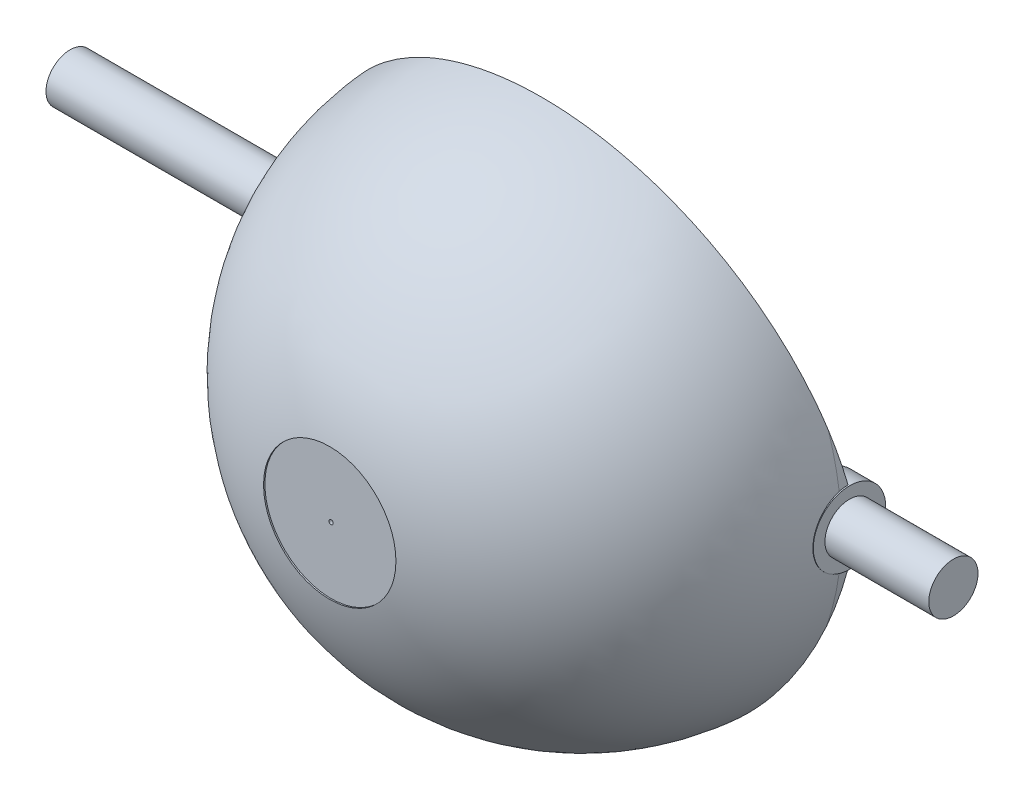
SolidWorks part; units mm, degrees
ref_plane "Front Plane" through (0, 0, 0) normal (0, 0, 1) x (1, 0, 0)
ref_plane "Top Plane" through (0, 0, 0) normal (0, 1, 0) x (1, 0, 0)
ref_plane "Right Plane" through (0, 0, 0) normal (1, 0, 0) x (0, 0, -1)
sketch "Sketch1" plane through (0, 0, 0) normal (0, 0, 1) x (1, 0, 0)
  circle A0 centre (0, 0) radius 27.95
extrude "Boss-Extrude1" add sketch "Sketch1" along normal blind 27.6202
fillet "Fillet1" radius 26.67 1 edges at (27.95, 0, 27.6202)
shell "Shell1" thickness 1.778
sketch "Sketch3" plane through (0, 0, 0) normal (0, 0, -1) x (-1, 0, 0)
  line L1 (-28.5123, -1.3772) -> (-25.5345, -1.3772)
  line L2 (-28.5123, -1.3772) -> (-28.5123, 1.3772)
  line L3 (-28.5123, 1.3772) -> (-25.5345, 1.3772)
  line L4 (-25.5345, -1.3772) -> (-25.5345, 1.3772)
  line L5 (-28.5123, -1.3772) -> (-25.5345, 1.3772) construction
  line L6 (-28.5123, 1.3772) -> (-25.5345, -1.3772) construction
  point P0 (-27.0234, 0)
extrude "Boss-Extrude3" add sketch "Sketch3" along normal blind 1.016
sketch "Sketch4" plane through (28.5123, 0, 0) normal (1, 0, 0) x (0, 0, -1)
  circle A0 centre (0, 0) radius 3.8203
extrude "Boss-Extrude4" add sketch "Sketch4" against normal blind 82.9108 and the other way blind 10.2887 contours A0
sketch "Sketch5" plane through (-54.3985, 0, 0) normal (-1, 0, 0) x (0, 0, 1)
  circle A1 centre (0, 0) radius 0.2185
extrude "Cut-Extrude1" cut sketch "Sketch5" against normal blind 74.422
sketch "Sketch6" plane through (-54.3985, 0, 0) normal (-1, 0, 0) x (0, 0, 1)
  circle A0 centre (0, 0) radius 4.4527
  circle A1 centre (0, 0) radius 2.5419
extrude "Cut-Extrude2" cut sketch "Sketch6" against normal blind 26.4656 contours A1 | A0
sketch "Sketch7" plane through (38.8009, 0, 0) normal (1, 0, 0) x (0, 0, -1)
  circle A0 centre (0, 0) radius 4.5798
  circle A1 centre (0, 0) radius 2.5953
extrude "Cut-Extrude3" cut sketch "Sketch7" against normal blind 10.9598 contours A1 | A0
sketch "Sketch9" plane through (0, 0, 0) normal (0, 0, -1) x (-1, 0, 0)
  circle A0 centre (0, 0) radius 25.3275
extrude "Cut-Extrude4" cut sketch "Sketch9" against normal blind 4.572 and the other way blind 8.128
sketch "Sketch10" plane through (0, 0, 27.6202) normal (0, 0, 1) x (1, 0, 0)
  circle A0 centre (0, 0) radius 0.2266
extrude "Cut-Extrude5" cut sketch "Sketch10" against normal blind 5.588 contours A0
sketch3d "3DSketch1"
  circle A0 centre (0, 0, 27.5994) radius 0.2266 construction
  point P2 (0, 0, 27.3728)
sketch "Sketch11" plane through (0, 0, 27.5994) normal (0, 0, 1) x (1, 0, 0)
  circle A0 centre (0, 0) radius 0.9577
extrude "Boss-Extrude5" add sketch "Sketch11" against normal blind 22.86 separate body contours A0
sketch "Sketch12" plane through (0, 0, 4.7394) normal (0, 0, -1) x (-1, 0, 0)
  line L0 (0, 0) -> (0, 16.6384)
  line L1 (0, 16.6384) -> (11.938, 16.6384)
  line L2 (0, 0) -> (0, -16.6384)
  line L3 (0, -16.6384) -> (-11.9535, -16.6384)
  circle A0 centre (11.938, 16.6384) radius 3.048
  circle A1 centre (-11.9535, -16.6384) radius 3.048
extrude "Boss-Extrude6" add sketch "Sketch12" against normal blind 10.7843 separate body contours A0 | A1
sketch "Sketch14" plane through (0, 0, 0) normal (0, 0, -1) x (-1, 0, 0)
  circle A0 centre (0, 0) radius 27.95
  circle A1 centre (0, 0) radius 2.1119
extrude "Cut-Extrude6" cut sketch "Sketch14" against normal blind 33.274 contours A1
sketch "Sketch15" plane through (38.8009, 0, 0) normal (1, 0, 0) x (0, 0, -1)
  line L0 (0, 3.8203) -> (-4.8913, 29.145)
  line L1 (-4.8913, 29.145) -> (1.6598, 29.145)
  line L2 (1.6598, 29.145) -> (0, 3.8203)
  circle A0 centre (0, 0) radius 3.8203 construction
extrude "Cut-Extrude7" cut sketch "Sketch15" against normal blind 66.802
sketch "Sketch16" plane through (38.8009, 0, 0) normal (1, 0, 0) x (0, 0, -1)
  line L0 (0, -3.8203) -> (-4.2889, -28.4863)
  line L1 (-4.2889, -28.4863) -> (3.8203, -28.4863)
  line L2 (3.8203, -28.4863) -> (0, -3.8203)
extrude "Cut-Extrude8" cut sketch "Sketch16" against normal blind 66.802
sketch "Sketch17" plane through (0, 0, 27.6202) normal (0, 0, 1) x (1, 0, 0)
  circle A0 centre (0, 0) radius 6.985
extrude "Cut-Extrude9" cut sketch "Sketch17" against normal blind 0.762
sketch "Sketch18" plane through (0, 0, 4.7394) normal (0, 0, -1) x (-1, 0, 0)
  line L0 (9.3966, 18.3211) -> (12.8563, 23.5463)
  line L1 (12.8563, 23.5463) -> (17.4529, 20.5028)
  line L2 (17.4529, 20.5028) -> (14.4794, 14.9557)
  line L3 (14.4794, 14.9557) -> (9.3966, 18.3211)
  circle A0 centre (11.938, 16.6384) radius 3.048 construction
extrude "Boss-Extrude7" add sketch "Sketch18" against normal blind 3.302
sketch "Sketch19" plane through (0, 0, 4.7394) normal (0, 0, -1) x (-1, 0, 0)
  line L0 (-14.4983, -14.9608) -> (-17.6135, -19.6864)
  line L1 (-17.6135, -19.6864) -> (-12.9382, -22.6256)
  line L2 (-12.9382, -22.6256) -> (-9.6014, -18.5769)
  line L3 (-9.6014, -18.5769) -> (-14.4983, -14.9608)
  circle A0 centre (-11.9535, -16.6384) radius 3.048 construction
  spline S0 degree 3 poles (-24.4696, -9.2851) (-24.003, -10.5148) (-23.4474, -11.6935) (-22.1656, -13.9533) (-21.4394, -15.0344) (-20.2188, -16.5808) (-19.7886, -17.0847) (-18.8984, -18.0505) (-18.4368, -18.5144) (-17.0036, -19.8503) (-15.9839, -20.6667) (-14.3569, -21.7791) (-13.7969, -22.1318) (-12.649, -22.7951) (-12.0658, -23.1031) (-10.2891, -23.9583) (-9.0686, -24.437) (-7.1841, -25.0185) (-6.5469, -25.1895) (-5.2541, -25.4846) (-4.5983, -25.6085) (-2.6367, -25.9035) (-1.3256, -26.0011) (0.6458, -26.002) (1.3037, -25.9779) (2.6213, -25.8802) (3.2833, -25.8061) (5.2542, -25.5101) (7.821, -24.9236) (10.2697, -23.967) (12.0604, -23.1061) (12.6481, -22.7955) (13.7884, -22.1368) (14.3435, -21.7876) (15.9641, -20.6814) (16.9854, -19.866) (18.4271, -18.524) (18.8945, -18.0546) (19.7873, -17.0864) (20.2125, -16.5882) (21.4259, -15.0527) (22.1524, -13.9744) (23.1181, -12.2751) (23.4192, -11.6949) (23.9788, -10.5064) (24.2363, -9.9) (24.4696, -9.2851) knots 0 0 0 0 0.0625 0.0625 0.125 0.125 0.15625 0.15625 0.1875 0.1875 0.25 0.25 0.28125 0.28125 0.3125 0.3125 0.375 0.375 0.40625 0.40625 0.4375 0.4375 0.5 0.5 0.53125 0.53125 0.5625 0.5625 0.625 0.6875 0.6875 0.71875 0.71875 0.75 0.75 0.8125 0.8125 0.84375 0.84375 0.875 0.875 0.9375 0.9375 0.96875 0.96875 1 1 1 1 construction
extrude "Boss-Extrude8" add sketch "Sketch19" against normal blind 4.572
